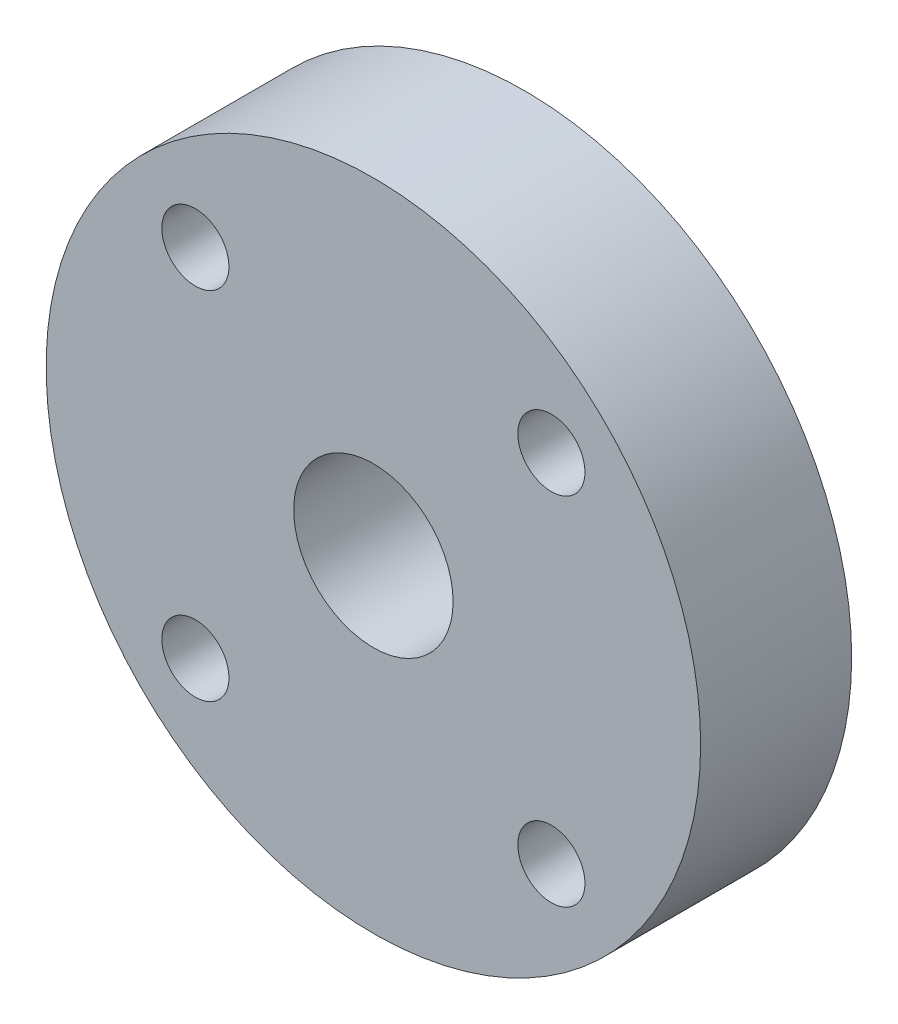
SolidWorks part; units mm, degrees
ref_plane "Front Plane" through (0, 0, 0) normal (0, 0, 1) x (1, 0, 0)
ref_plane "Top Plane" through (0, 0, 0) normal (0, 1, 0) x (1, 0, 0)
ref_plane "Right Plane" through (0, 0, 0) normal (1, 0, 0) x (0, 0, -1)
sketch "Sketch1" plane through (0, 0, 0) normal (0, 0, 1) x (1, 0, 0)
  line L0 (0, 48.1938) -> (0, -53.492) construction
  line L1 (-34.8672, 34.8672) -> (0, 0) construction
  circle A0 centre (-21.2132, 21.2132) radius 4
  circle A2 centre (21.2132, 21.2132) radius 4
  circle A3 centre (21.2132, -21.2132) radius 4
  circle A4 centre (-21.2132, -21.2132) radius 4
  circle A5 centre (0, 0) radius 39
  circle A6 centre (0, 0) radius 9.5
  point P20 (0, 0)
  dimension "D1" = 8
  dimension "D2" = 78
  dimension "D5" = 19
  dimension "D3" = 45
  dimension "D4" = 4
extrude "Boss-Extrude1" add sketch "Sketch1" along normal blind 18
